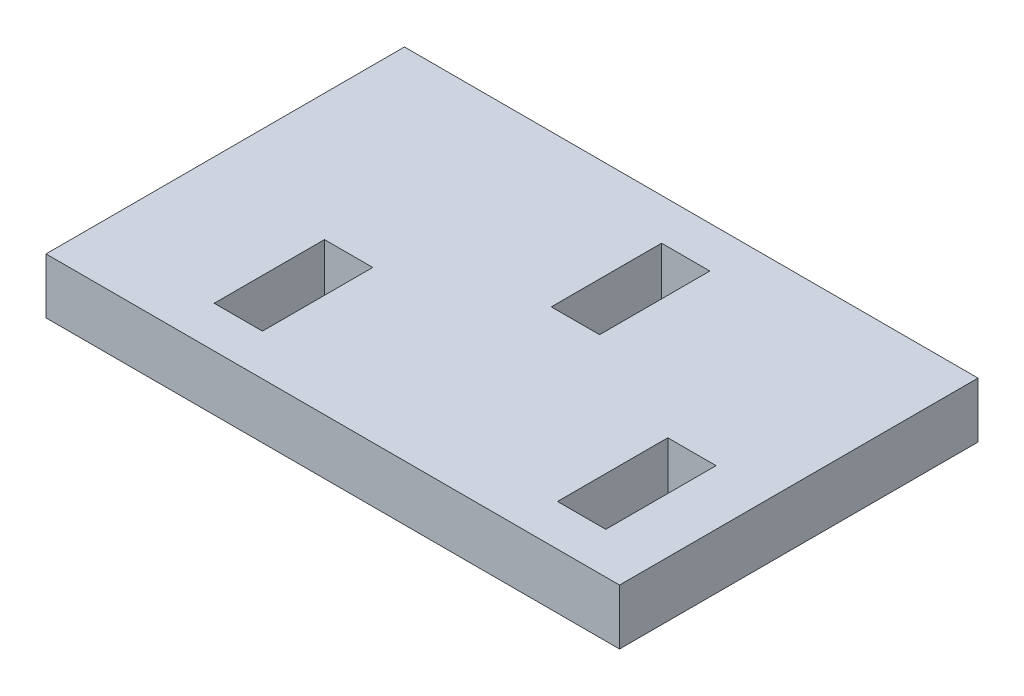
SolidWorks part; units mm, degrees
ref_plane "Front Plane" through (0, 0, 0) normal (0, 0, 1) x (1, 0, 0)
ref_plane "Top Plane" through (0, 0, 0) normal (0, 1, 0) x (1, 0, 0)
ref_plane "Right Plane" through (0, 0, 0) normal (1, 0, 0) x (0, 0, -1)
sketch "Sketch1" plane through (0, 0, 0) normal (0, 1, 0) x (1, 0, 0)
  line L1 (-26.416, -16.51) -> (26.416, -16.51)
  line L2 (-26.416, -16.51) -> (-26.416, 16.51)
  line L3 (-26.416, 16.51) -> (26.416, 16.51)
  line L4 (26.416, -16.51) -> (26.416, 16.51)
  line L5 (-26.416, -16.51) -> (26.416, 16.51) construction
  line L6 (-26.416, 16.51) -> (26.416, -16.51) construction
  point P0 (0, 0)
  dimension "D1" = 33.02
  dimension "D2" = 52.832
extrude "Boss-Extrude1" add sketch "Sketch1" along normal blind 5.1054
sketch "Sketch2" plane through (0, 5.1054, 0) normal (0, 1, 0) x (1, 0, 0)
  line L0 (16.891, -12.7) -> (16.891, -2.54) construction
  line L1 (16.891, -2.54) -> (21.336, -2.54) construction
  line L2 (21.336, -2.54) -> (21.336, -12.7) construction
  line L3 (21.336, -12.7) -> (16.891, -12.7) construction
  line L4 (5.5245, 2.54) -> (1.0795, 2.54) construction
  line L5 (5.5245, 12.7) -> (5.5245, 2.54) construction
  line L6 (1.0795, 12.7) -> (5.5245, 12.7) construction
  line L7 (1.0795, 2.54) -> (1.0795, 12.7) construction
  line L8 (-10.287, -2.54) -> (-10.287, -12.7) construction
  line L9 (-14.732, -12.7) -> (-14.732, -2.54) construction
  line L10 (-10.287, -12.7) -> (-14.732, -12.7) construction
  line L11 (-14.732, -2.54) -> (-10.287, -2.54) construction
  line L12 (16.891, -12.7) -> (16.891, -2.54)
  line L13 (16.891, -2.54) -> (21.336, -2.54)
  line L14 (21.336, -2.54) -> (21.336, -12.7)
  line L15 (21.336, -12.7) -> (16.891, -12.7)
  line L16 (5.5245, 2.54) -> (1.0795, 2.54)
  line L17 (5.5245, 12.7) -> (5.5245, 2.54)
  line L18 (1.0795, 12.7) -> (5.5245, 12.7)
  line L19 (1.0795, 2.54) -> (1.0795, 12.7)
  line L20 (-10.287, -2.54) -> (-10.287, -12.7)
  line L21 (-14.732, -12.7) -> (-14.732, -2.54)
  line L22 (-10.287, -12.7) -> (-14.732, -12.7)
  line L23 (-14.732, -2.54) -> (-10.287, -2.54)
extrude "Cut-Extrude1" cut sketch "Sketch2" against normal through all
equation "\"material\"=\"FoamCore@Platform.assembly\""
equation "\"D1@Boss-Extrude1\"=\"material\""
